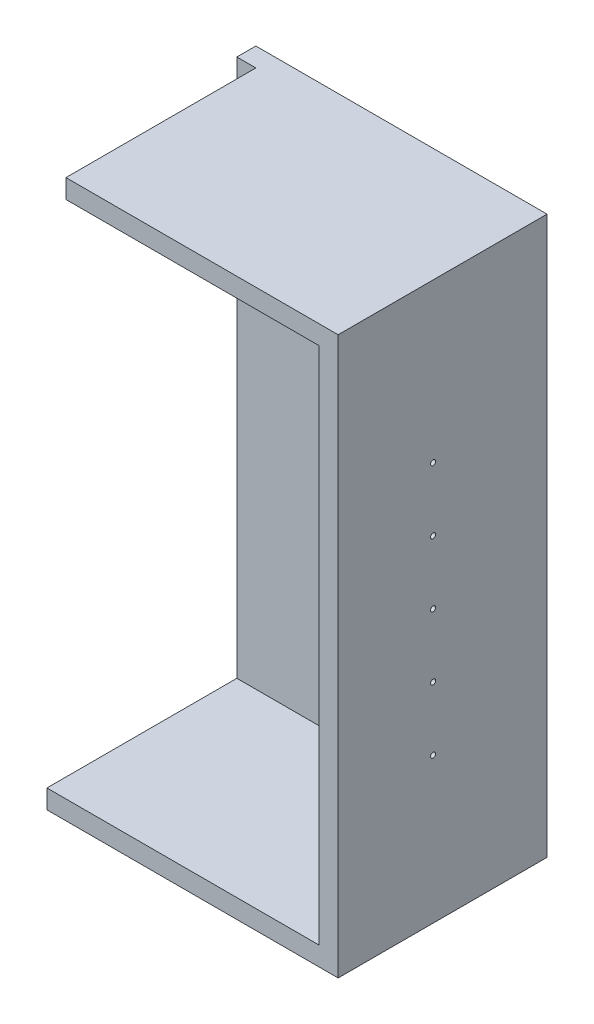
SolidWorks part; units mm, degrees
ref_plane "Front Plane" through (0, 0, 0) normal (0, 0, 1) x (1, 0, 0)
ref_plane "Top Plane" through (0, 0, 0) normal (0, 1, 0) x (1, 0, 0)
ref_plane "Right Plane" through (0, 0, 0) normal (1, 0, 0) x (0, 0, -1)
sketch "Sketch1" plane through (0, 0, 0) normal (0, 0, 1) x (1, 0, 0)
  line L0 (-230, -440) -> (-230, 440)
  line L1 (-200, -410) -> (200, -410)
  line L2 (-200, -410) -> (-200, 410)
  line L3 (-200, 410) -> (200, 410)
  line L4 (200, -410) -> (200, 410)
  line L5 (-200, -410) -> (200, 410) construction
  line L6 (-200, 410) -> (200, -410) construction
  line L7 (-230, 440) -> (230, 440)
  line L8 (230, -440) -> (230, 440)
  line L9 (-230, -440) -> (230, -440)
  point P0 (0, 0)
  dimension "D1" = 820
  dimension "D2" = 400
  dimension "D3" = 30
extrude "Boss-Extrude1" add sketch "Sketch1" along normal blind 300
sketch "Sketch2" plane through (0, 0, 0) normal (0, 0, -1) x (-1, 0, 0)
  line L1 (-230, 440) -> (230, 440)
  line L2 (-230, 440) -> (-230, -440)
  line L3 (-230, -440) -> (230, -440)
  line L4 (230, 440) -> (230, -440)
extrude "Boss-Extrude2" add sketch "Sketch2" along normal blind 30
sketch "Sketch3" plane through (230, 0, 0) normal (1, 0, 0) x (0, 0, -1)
  line L0 (-300, 440) -> (30, 440) construction
  line L1 (-300, -440) -> (-300, 440) construction
  circle A0 centre (-150, 190) radius 4
  circle A1 centre (-150, 90) radius 4
  circle A2 centre (-150, -10) radius 4
  circle A3 centre (-150, -110) radius 4
  circle A4 centre (-150, -210) radius 4
  dimension "D1" = 250
  dimension "D3" = 100
  dimension "D5" = 100
  dimension "D6" = 100
  dimension "D2" = 150
  dimension "D4" = 100
extrude "Cut-Extrude1" cut sketch "Sketch3" against normal up to surface (460 mm away) up to face at (-230, 0, 135)
sketch "Sketch4" plane through (0, 0, 300) normal (0, 0, 1) x (1, 0, 0)
  line L1 (-230, 440) -> (-200, 440)
  line L2 (-230, 440) -> (-230, -410)
  line L3 (-230, -410) -> (-200, -410)
  line L4 (-200, 440) -> (-200, -410)
extrude "Cut-Extrude2" cut sketch "Sketch4" against normal up to surface (300 mm away) up to face at (0, 0, 0)
